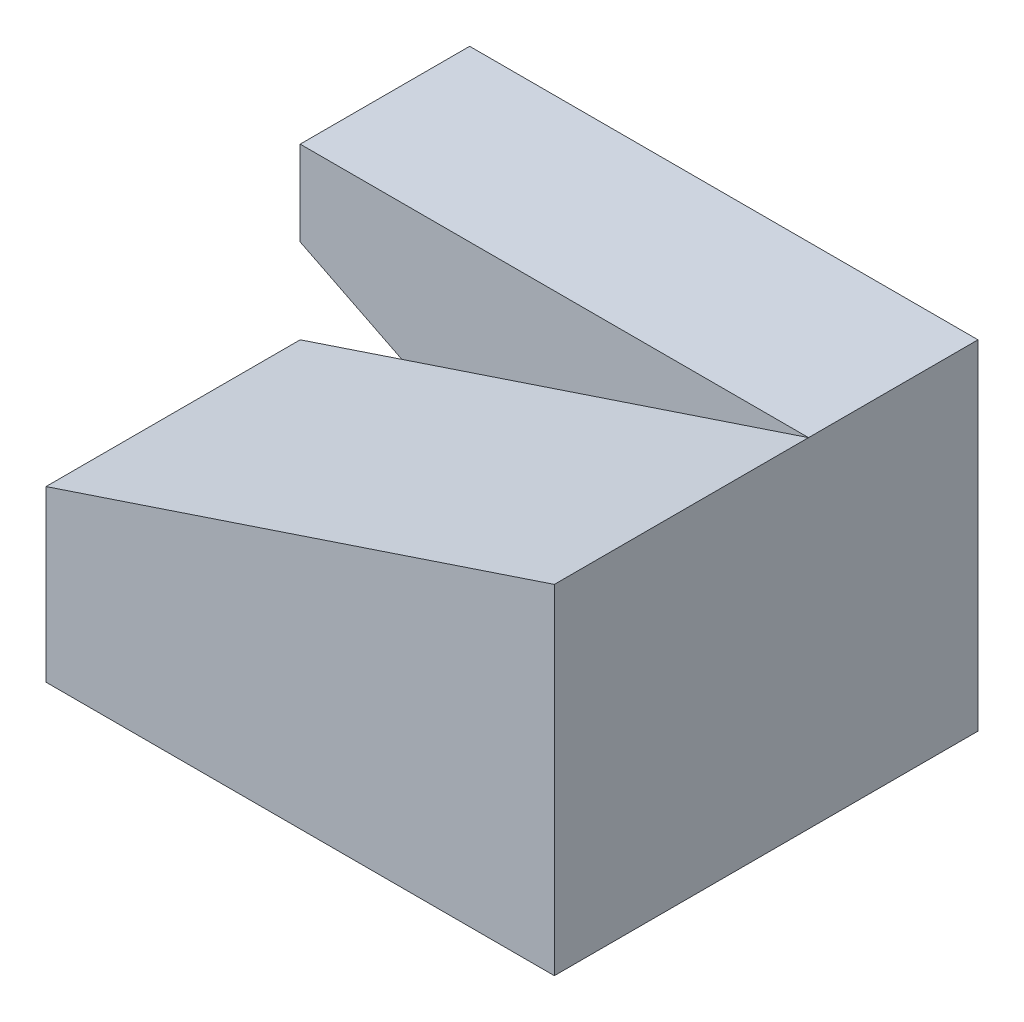
SolidWorks part; units mm, degrees
ref_plane "Front Plane" through (0, 0, 0) normal (0, 0, 1) x (1, 0, 0)
ref_plane "Top Plane" through (0, 0, 0) normal (0, 1, 0) x (1, 0, 0)
ref_plane "Right Plane" through (0, 0, 0) normal (1, 0, 0) x (0, 0, -1)
sketch "Sketch1" plane through (0, 0, 0) normal (0, 0, 1) x (1, 0, 0)
  line L0 (-36.7521, 6.2821) -> (-36.7521, -3.7179)
  line L1 (-36.7521, -3.7179) -> (-6.7521, -3.7179)
  line L2 (-6.7521, -3.7179) -> (-6.7521, 16.2821)
  line L3 (-6.7521, 16.2821) -> (-36.7521, 6.2821)
  dimension "D1" = 10
  dimension "D2" = 30
  dimension "D3" = 20
extrude "Boss-Extrude1" add sketch "Sketch1" along normal blind 15
sketch "Sketch2" plane through (0, 0, 0) normal (0, 0, -1) x (-1, 0, 0)
  line L0 (6.7521, -3.7179) -> (6.7521, 16.2821)
  line L1 (6.7521, -3.7179) -> (6.7521, 16.2821) construction
  line L2 (6.7521, 16.2821) -> (36.7521, 16.2821)
  line L3 (36.7521, 16.2821) -> (36.7521, 11.2821)
  line L4 (36.7521, 11.2821) -> (6.7521, -3.7179)
  dimension "D1" = 5
  dimension "D2" = 20
extrude "Boss-Extrude2" add sketch "Sketch2" along normal blind 10
